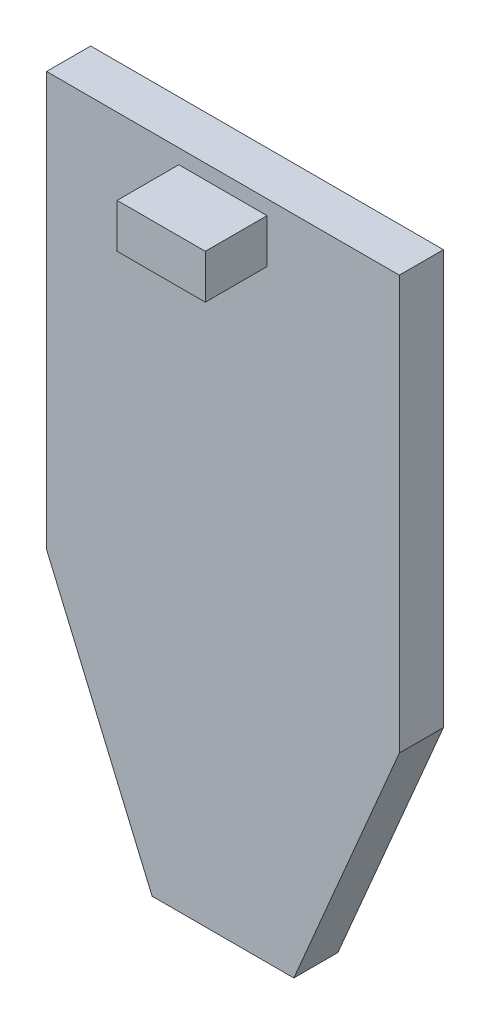
SolidWorks part; units mm, degrees
ref_plane "Front Plane" through (0, 0, 0) normal (0, 0, 1) x (1, 0, 0)
ref_plane "Top Plane" through (0, 0, 0) normal (0, 1, 0) x (1, 0, 0)
ref_plane "Right Plane" through (0, 0, 0) normal (1, 0, 0) x (0, 0, -1)
sketch "Sketch1" plane through (0, 0, 0) normal (0, 0, 1) x (1, 0, 0)
  line L0 (0, 23.1844) -> (0, -26.6805) construction
  line L1 (-4, 6.5628) -> (4, 6.5628)
  line L2 (-4, 6.5628) -> (-4, -2.8231)
  line L3 (-1.607, -8.4372) -> (1.607, -8.4372)
  line L4 (4, 6.5628) -> (4, -2.8231)
  line L5 (4, -2.8231) -> (1.607, -8.4372)
  line L6 (-4, -2.8231) -> (-1.607, -8.4372)
  dimension "D2" = 8
extrude "Boss-Extrude1" add sketch "Sketch1" along normal blind 1
sketch "Sketch2" plane through (0, 0, 1) normal (0, 0, 1) x (1, 0, 0)
  line L0 (0, 7.9476) -> (0, -11.1031) construction
  line L2 (-1, 6.2312) -> (1, 6.2312)
  line L3 (-1, 6.2312) -> (-1, 5.2312)
  line L4 (-1, 5.2312) -> (1, 5.2312)
  line L5 (1, 6.2312) -> (1, 5.2312)
  dimension "D1" = 2
  dimension "D2" = 1
extrude "Boss-Extrude2" add sketch "Sketch2" along normal blind 1.4
